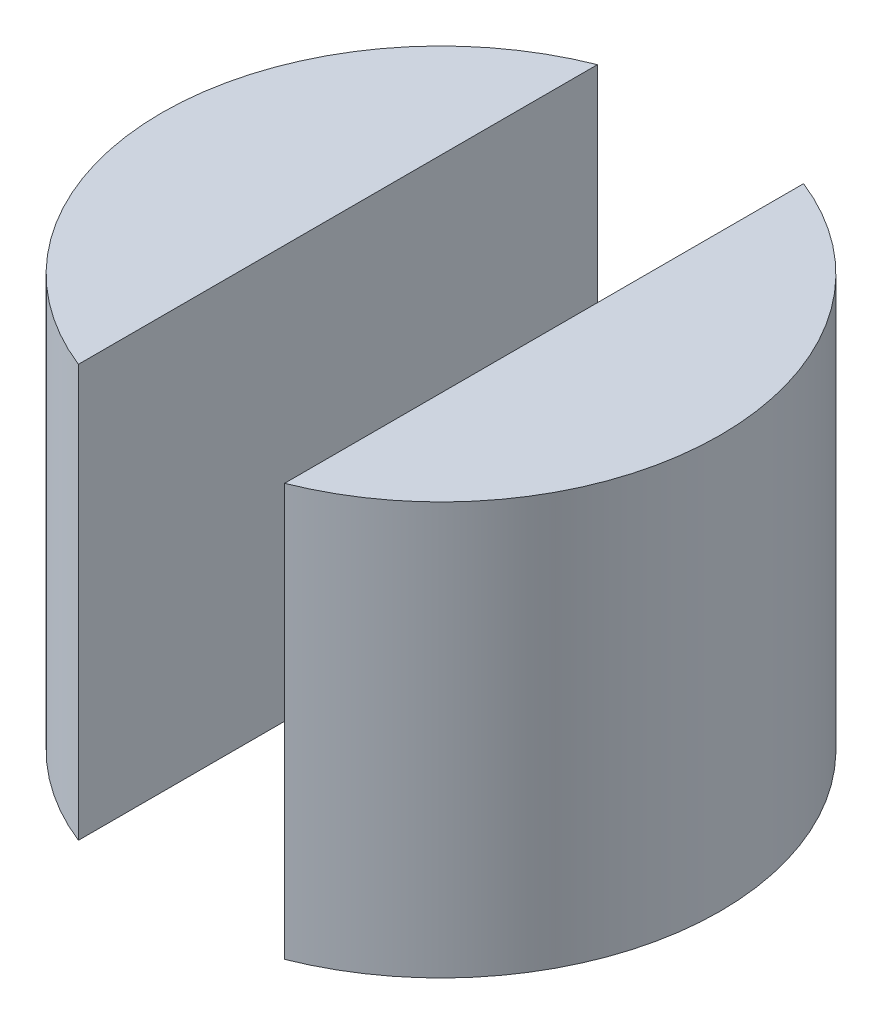
SolidWorks part; units mm, degrees
ref_plane "Front Plane" through (0, 0, 0) normal (0, 0, 1) x (1, 0, 0)
ref_plane "Top Plane" through (0, 0, 0) normal (0, 1, 0) x (1, 0, 0)
ref_plane "Right Plane" through (0, 0, 0) normal (1, 0, 0) x (0, 0, -1)
sketch "Sketch2" plane through (0, 0, 0) normal (0, 1, 0) x (1, 0, 0)
  line L0 (-1.5, 3.777) -> (-1.5, -3.777)
  line L1 (1.5, 3.777) -> (1.5, -3.777)
  arc A0 (-1.5, 3.777) -> (-1.5, -3.777) centre (0, 0) ccw
  arc A1 (1.5, -3.777) -> (1.5, 3.777) centre (0, 0) ccw
  dimension "D1" = 3
extrude "Boss-Extrude1" add sketch "Sketch2" along normal blind 6
